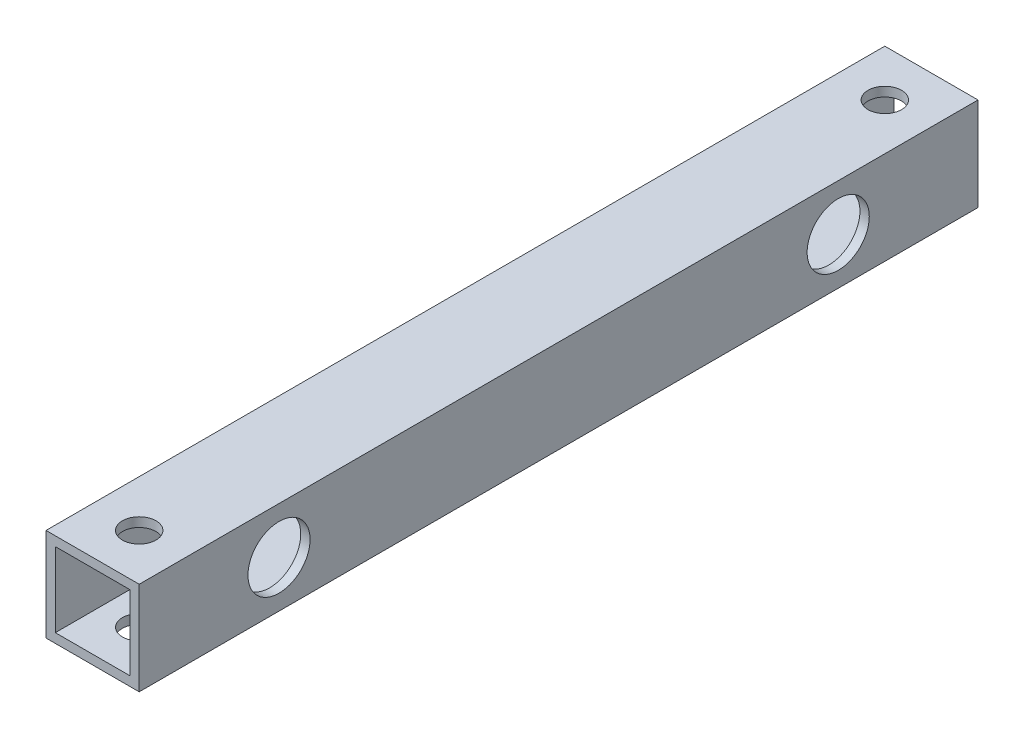
SolidWorks part; units mm, degrees
material "6063-T5"
ref_plane "正面" through (0, 0, 0) normal (0, 0, 1) x (1, 0, 0)
ref_plane "平面" through (0, 0, 0) normal (0, 1, 0) x (1, 0, 0)
ref_plane "右側面" through (0, 0, 0) normal (1, 0, 0) x (0, 0, -1)
sketch "ｽｹｯﾁ1" plane through (0, 0, 0) normal (0, 0, 1) x (1, 0, 0)
  line L1 (-7.5, -7.5) -> (7.5, -7.5)
  line L2 (-7.5, -7.5) -> (-7.5, 7.5)
  line L3 (-7.5, 7.5) -> (7.5, 7.5)
  line L4 (7.5, -7.5) -> (7.5, 7.5)
  line L5 (-7.5, -7.5) -> (7.5, 7.5) construction
  line L6 (-7.5, 7.5) -> (7.5, -7.5) construction
  line L7 (-6, -6) -> (6, -6)
  line L8 (-6, -6) -> (-6, 6)
  line L9 (-6, 6) -> (6, 6)
  line L10 (6, -6) -> (6, 6)
  line L11 (-6, -6) -> (6, 6) construction
  line L12 (-6, 6) -> (6, -6) construction
  point P0 (0, 0)
  point P6 (0, 0)
  dimension "D1" = 1.5
  dimension "D2" = 15
  dimension "D3" = 15
extrude "ﾎﾞｽ - 押し出し1" add sketch "ｽｹｯﾁ1" along normal blind 135
sketch "ｽｹｯﾁ2" plane through (7.5, 0, 0) normal (1, 0, 0) x (0, 0, -1)
  line L0 (-135, -7.5) -> (0, -7.5) construction
  line L2 (-135, -7.5) -> (-135, 7.5) construction
  circle A4 centre (-112.5, 0) radius 2.7
  circle A8 centre (-22.5, 0) radius 2.7
  dimension "D1" = 5.4
  dimension "D2" = 22.5
  dimension "D3" = 7.5
  dimension "D4" = 90
  dimension "D9" = 2
extrude "ｶｯﾄ - 押し出し1" cut sketch "ｽｹｯﾁ2" against normal blind 25
sketch "ｽｹｯﾁ3" plane through (0, 7.5, 0) normal (0, 1, 0) x (1, 0, 0)
  line L2 (7.5, -135) -> (7.5, 0) construction
  circle A1 centre (0, -7.5) radius 2.7
  circle A6 centre (0, -127.5) radius 2.7
  dimension "D2" = 120
  dimension "D3" = 5.4
  dimension "D9" = 7.5
  dimension "D11" = 7.5
  dimension "D4" = 7.5
  dimension "D5" = 5.4
extrude "ｶｯﾄ - 押し出し2" cut sketch "ｽｹｯﾁ3" against normal blind 25
sketch "ｽｹｯﾁ5" plane through (7.5, 0, 0) normal (1, 0, 0) x (0, 0, -1)
  circle A0 centre (-22.5, 0) radius 5
  circle A1 centre (-112.5, 0) radius 5
  dimension "D1" = 10
  dimension "D2" = 10
extrude "ｶｯﾄ - 押し出し4" cut sketch "ｽｹｯﾁ5" against normal blind 10
